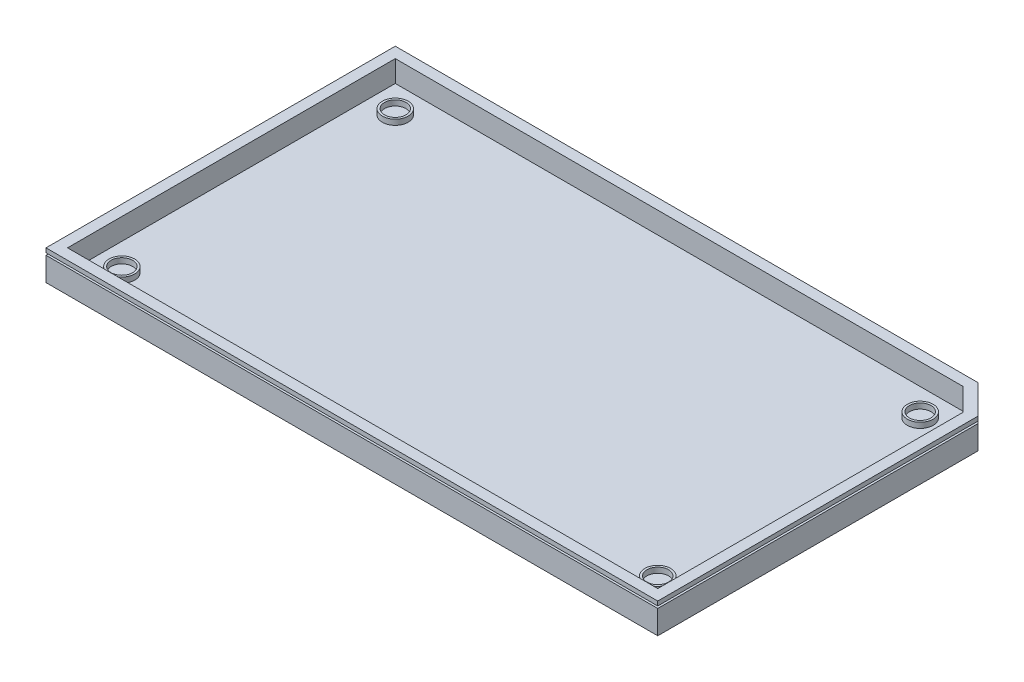
SolidWorks part; units mm, degrees
ref_plane "Front Plane" through (0, 0, 0) normal (0, 0, 1) x (1, 0, 0)
ref_plane "Top Plane" through (0, 0, 0) normal (0, 1, 0) x (1, 0, 0)
ref_plane "Right Plane" through (0, 0, 0) normal (1, 0, 0) x (0, 0, -1)
sketch "Sketch1" plane through (0, 0, 0) normal (0, 1, 0) x (1, 0, 0)
  line L0 (64.135, -35.56) -> (64.135, 31.75) construction
  line L2 (-64.135, 35.56) -> (-64.135, -35.56)
  line L3 (-64.135, -35.56) -> (67.945, -35.56)
  line L5 (-64.135, 31.75) -> (64.135, 31.75) construction
  line L8 (64.135, 35.56) -> (67.945, 31.75)
  line L9 (64.135, 35.56) -> (-64.135, 35.56)
  line L10 (67.945, 31.75) -> (67.945, -35.56)
  point P6 (-64.135, 0)
  point P10 (0, 35.56)
  dimension "D1" = 45
  dimension "D2" = 71.12
  dimension "D3" = 67.31
  dimension "D4" = 128.27
sketch "Sketch2" plane through (0, 0, 0) normal (0, 1, 0) x (1, 0, 0)
  line L19 (-1.4645, 40.56) -> (-1.4645, -40.56) construction
  line L20 (-69.135, 0) -> (72.945, 0) construction
  line L21 (-64.135, 35.56) -> (-64.135, -35.56) construction
  line L22 (-64.135, -35.56) -> (67.945, -35.56) construction
  line L23 (67.945, 31.75) -> (67.945, -35.56) construction
  line L24 (-69.135, -40.56) -> (72.945, -40.56)
  line L25 (72.945, -40.56) -> (72.945, 33.8211)
  line L26 (72.945, 33.8211) -> (66.2061, 40.56)
  line L27 (66.2061, 40.56) -> (-69.135, 40.56)
  line L28 (-69.135, 40.56) -> (-69.135, -40.56)
  line L29 (-69.135, -40.56) -> (72.945, -40.56)
  line L30 (72.945, -40.56) -> (72.945, 33.8211)
  line L31 (72.945, 33.8211) -> (66.2061, 40.56)
  line L32 (66.2061, 40.56) -> (-69.135, 40.56)
  line L33 (-69.135, 40.56) -> (-69.135, -40.56)
  line L34 (-64.135, 31.75) -> (64.135, 31.75) construction
  circle A0 centre (-60.325, -31.75) radius 2.5
  circle A1 centre (-60.325, 31.75) radius 2.5
  circle A2 centre (64.135, -31.75) radius 2.5
  circle A3 centre (61.595, 31.75) radius 2.5
  dimension "D2" = 5
  dimension "D5" = 5
  dimension "D9" = 5
  dimension "D3" = 3.81
  dimension "D4" = 3.81
  dimension "D6" = 3.81
  dimension "D7" = 3.81
  dimension "D8" = 6.35
  dimension "D1" = 5
sketch "Sketch3" plane through (0, 0, 0) normal (0, 1, 0) x (1, 0, 0)
  line L0 (72.945, 33.8211) -> (66.2061, 40.56) construction
  line L1 (72.945, -40.56) -> (72.945, 33.8211) construction
  line L2 (-69.135, -40.56) -> (72.945, -40.56) construction
  line L3 (66.2061, 40.56) -> (-69.135, 40.56) construction
  line L4 (-69.135, 40.56) -> (-69.135, -40.56) construction
  line L5 (72.945, 33.8211) -> (66.2061, 40.56)
  line L6 (72.945, -40.56) -> (72.945, 33.8211)
  line L7 (-69.135, -40.56) -> (72.945, -40.56)
  line L8 (66.2061, 40.56) -> (-69.135, 40.56)
  line L9 (-69.135, 40.56) -> (-69.135, -40.56)
sketch "Sketch4" plane through (0, 0, 0) normal (0, 1, 0) x (1, 0, 0)
  line L24 (-66.635, -38.06) -> (70.445, -38.06)
  line L25 (70.445, -38.06) -> (70.445, 32.7855)
  line L26 (70.445, 32.7855) -> (65.1705, 38.06)
  line L27 (65.1705, 38.06) -> (-66.635, 38.06)
  line L28 (-66.635, 38.06) -> (-66.635, -38.06)
  line L29 (-66.635, -38.06) -> (70.445, -38.06)
  line L30 (70.445, -38.06) -> (70.445, 32.7855)
  line L31 (70.445, 32.7855) -> (65.1705, 38.06)
  line L32 (65.1705, 38.06) -> (-66.635, 38.06)
  line L33 (-66.635, 38.06) -> (-66.635, -38.06)
  dimension "D1" = 2.5
sketch "Sketch5" plane through (0, 0, 0) normal (0, 1, 0) x (1, 0, 0)
  circle A0 centre (61.595, 31.75) radius 2.5 construction
  circle A1 centre (64.135, -31.75) radius 2.5 construction
  circle A2 centre (-60.325, -31.75) radius 2.5 construction
  circle A3 centre (-60.325, 31.75) radius 2.5 construction
  circle A4 centre (61.595, 31.75) radius 2.5
  circle A5 centre (64.135, -31.75) radius 2.5
  circle A6 centre (-60.325, -31.75) radius 2.5
  circle A7 centre (-60.325, 31.75) radius 2.5
  circle A8 centre (-60.325, -31.75) radius 3
  circle A9 centre (-60.325, 31.75) radius 3
  circle A10 centre (61.595, 31.75) radius 3
  circle A11 centre (64.135, -31.75) radius 3
  dimension "D1" = 6
  dimension "D2" = 6
  dimension "D3" = 6
  dimension "D4" = 6
extrude "Boss-Extrude1" add sketch "Sketch3" along normal blind 5 and the other way blind 2
extrude "Cut-Extrude1" cut sketch "Sketch4" along normal blind 5
extrude "Boss-Extrude2" add sketch "Sketch5" along normal blind 1.25 separate body
ref_plane "Plane1" through (0, 4, 0) normal (0, 1, 0) x (1, 0, 0)
sketch "Sketch6" plane through (0, 4, 0) normal (0, 1, 0) x (1, 0, 0)
  line L22 (-70.135, 41.56) -> (-70.135, -41.56)
  line L23 (-70.135, -41.56) -> (73.945, -41.56)
  line L24 (73.945, -41.56) -> (73.945, 34.2353)
  line L25 (73.945, 34.2353) -> (66.6203, 41.56)
  line L26 (66.6203, 41.56) -> (-70.135, 41.56)
  line L27 (-68.135, 39.56) -> (-68.135, -39.56)
  line L28 (-68.135, -39.56) -> (71.945, -39.56)
  line L29 (71.945, -39.56) -> (71.945, 33.4069)
  line L30 (71.945, 33.4069) -> (65.7919, 39.56)
  line L31 (65.7919, 39.56) -> (-68.135, 39.56)
  line L32 (-68.135, 39.56) -> (-68.135, -39.56)
  line L33 (-68.135, -39.56) -> (71.945, -39.56)
  line L34 (71.945, -39.56) -> (71.945, 33.4069)
  line L35 (71.945, 33.4069) -> (65.7919, 39.56)
  line L36 (65.7919, 39.56) -> (-68.135, 39.56)
  dimension "D1" = 1
  dimension "D2" = 2
extrude "Cut-Extrude2" cut sketch "Sketch6" against normal blind 0.5
ref_plane "Plane2" through (0, 9, 0) normal (0, 1, 0) x (1, 0, 0)
